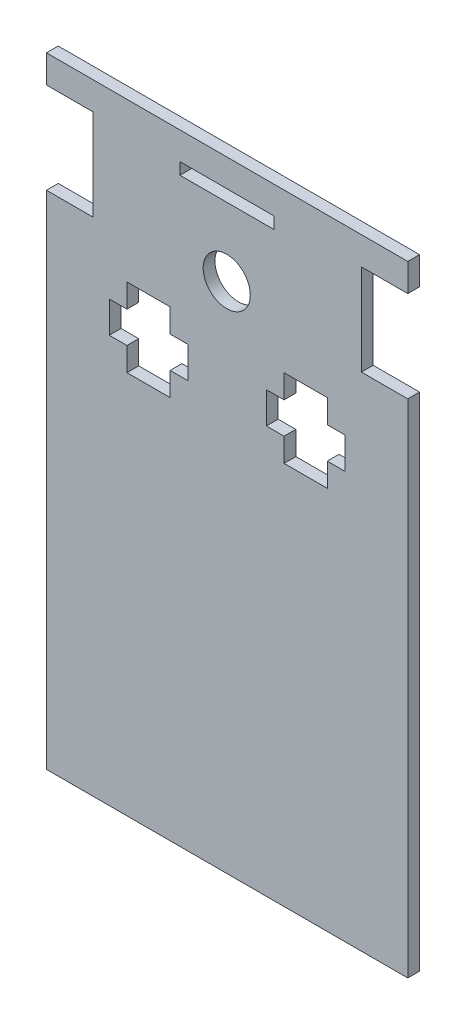
SolidWorks part; units mm, degrees
ref_plane "Alzado" through (0, 0, 0) normal (0, 0, 1) x (1, 0, 0)
ref_plane "Planta" through (0, 0, 0) normal (0, 1, 0) x (1, 0, 0)
ref_plane "Vista lateral" through (0, 0, 0) normal (1, 0, 0) x (0, 0, -1)
sketch "Model" plane through (0, 0, 0) normal (0, 0, 1) x (1, 0, 0)
  line L0 (54, 89) -> (54, 81.9)
  line L1 (146, 81.9) -> (146, 89)
  line L2 (134.2, 81.9) -> (146, 81.9)
  line L3 (134.2, 58.7) -> (134.2, 81.9)
  line L4 (146, 58.7) -> (134.2, 58.7)
  line L5 (146, -69) -> (146, 58.7)
  line L6 (54, -69) -> (146, -69)
  line L7 (54, 58.7) -> (54, -69)
  line L8 (146, 89) -> (54, 89)
  line L9 (65.8, 58.7) -> (54, 58.7)
  line L10 (65.8, 81.9) -> (65.8, 58.7)
  line L11 (54, 81.9) -> (65.8, 81.9)
  line L12 (88, 79) -> (112, 79)
  line L13 (88, 82) -> (88, 79)
  line L14 (112, 82) -> (88, 82)
  line L15 (112, 79) -> (112, 82)
  line L16 (85.5, 28.7216) -> (85.5, 34.7216)
  line L17 (125.5, 28.7216) -> (125.5, 34.7216)
  line L18 (74.5, 28.7216) -> (85.5, 28.7216)
  line L19 (114.5, 28.7216) -> (125.5, 28.7216)
  line L20 (74.5, 34.7216) -> (74.5, 28.7216)
  line L21 (114.5, 34.7216) -> (114.5, 28.7216)
  line L22 (90, 34.7216) -> (85.5, 34.7216)
  line L23 (130, 34.7216) -> (125.5, 34.7216)
  line L24 (90, 42.7216) -> (90, 34.7216)
  line L25 (130, 42.7216) -> (130, 34.7216)
  line L26 (85.5, 42.7216) -> (90, 42.7216)
  line L27 (125.5, 42.7216) -> (130, 42.7216)
  line L28 (85.5, 48.7216) -> (85.5, 42.7216)
  line L29 (125.5, 48.7216) -> (125.5, 42.7216)
  line L30 (74.5, 48.7216) -> (85.5, 48.7216)
  line L31 (114.5, 48.7216) -> (125.5, 48.7216)
  line L32 (74.5, 42.7216) -> (74.5, 48.7216)
  line L33 (114.5, 42.7216) -> (114.5, 48.7216)
  line L34 (70, 42.7216) -> (74.5, 42.7216)
  line L35 (110, 42.7216) -> (114.5, 42.7216)
  line L36 (70, 34.7216) -> (70, 42.7216)
  line L37 (110, 34.7216) -> (110, 42.7216)
  line L38 (74.5, 34.7216) -> (70, 34.7216)
  line L39 (114.5, 34.7216) -> (110, 34.7216)
  circle A0 centre (99.8993, 61.5296) radius 6
extrude "Saliente-Extruir1" add sketch "Model" along normal blind 3
